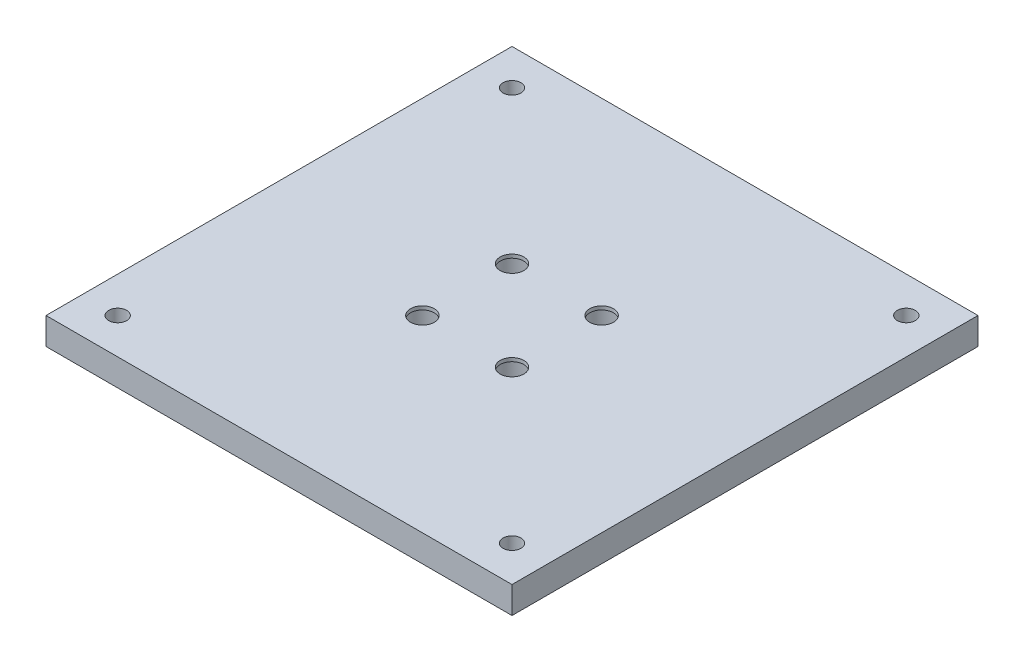
SolidWorks part; units mm, degrees
ref_plane "前视基准面" through (0, 0, 0) normal (0, 0, 1) x (1, 0, 0)
ref_plane "上视基准面" through (0, 0, 0) normal (0, 1, 0) x (1, 0, 0)
ref_plane "右视基准面" through (0, 0, 0) normal (1, 0, 0) x (0, 0, -1)
sketch "草图1" plane through (0, 0, 0) normal (0, 1, 0) x (1, 0, 0)
  line L1 (0, 0) -> (130, 0)
  line L2 (0, 0) -> (0, 130)
  line L3 (0, 130) -> (130, 130)
  line L4 (130, 0) -> (130, 130)
  dimension "D1" = 130
  dimension "D2" = 130
extrude "凸台-拉伸1" add sketch "草图1" along normal blind 7.5
sketch "草图2" plane through (0, 7.5, 0) normal (0, 1, 0) x (1, 0, 0)
  point P0 (10, 120)
  point P1 (120, 120)
  point P2 (10, 10)
  point P3 (120, 10)
  dimension "D1" = 110
  dimension "D2" = 110
hole_wizard "M6 螺纹孔2" positions "3D草图3" profile "草图4" tap size "M6" standard "GB" end condition through all
sketch3d "3D草图3"
  point P0 (10, 7.5, -120)
  point P3 (120, 7.5, -120)
  point P6 (120, 7.5, -10)
  point P9 (10, 7.5, -10)
sketch "草图4" plane through (10, 7.5, -120) normal (1, 0, 0) x (0, 0, 1)
  line L0 (0, 0) -> (0, 7.5)
  line L1 (0, 7.5) -> (2.5, 7.5)
  line L2 (2.5, 7.5) -> (2.5, 0)
  line L5 (2.5, 0) -> (0, 0)
  line L11 (0, -6.35) -> (0, 107.95) construction
  dimension "通孔螺纹孔钻头直径" = 5
  dimension "通孔螺纹孔钻头深度" = 7.5
cosmetic thread "孔螺蚊线5" parameters "D2"=6
cosmetic thread "孔螺蚊线6" parameters "D2"=6
cosmetic thread "孔螺蚊线7" parameters "D2"=6
cosmetic thread "孔螺蚊线8" parameters "D2"=6
sketch "草图6" plane through (0, 0, 0) normal (0, -1, 0) x (-1, 0, 0)
  circle A0 centre (-52.5, 52.5) radius 5.4
  circle A1 centre (-77.5, 52.5) radius 5.4
  circle A2 centre (-52.5, 77.5) radius 5.4
  circle A3 centre (-77.5, 77.5) radius 5.4
  dimension "D1" = 10.8
  dimension "D3" = 10.8
  dimension "D2" = 25
  dimension "D4" = 25
extrude "切除-拉伸1" cut sketch "草图6" against normal blind 6.5
sketch "草图7" plane through (0, 6.5, 0) normal (0, -1, 0) x (1, 0, 0)
  circle A0 centre (52.5, -52.5) radius 3.3
  circle A1 centre (77.5, -52.5) radius 3.3
  circle A2 centre (77.5, -77.5) radius 3.3
  circle A3 centre (52.5, -77.5) radius 3.3
  dimension "D1" = 6.6
  dimension "D2" = 6.6
extrude "切除-拉伸2" cut sketch "草图7" against normal through all
